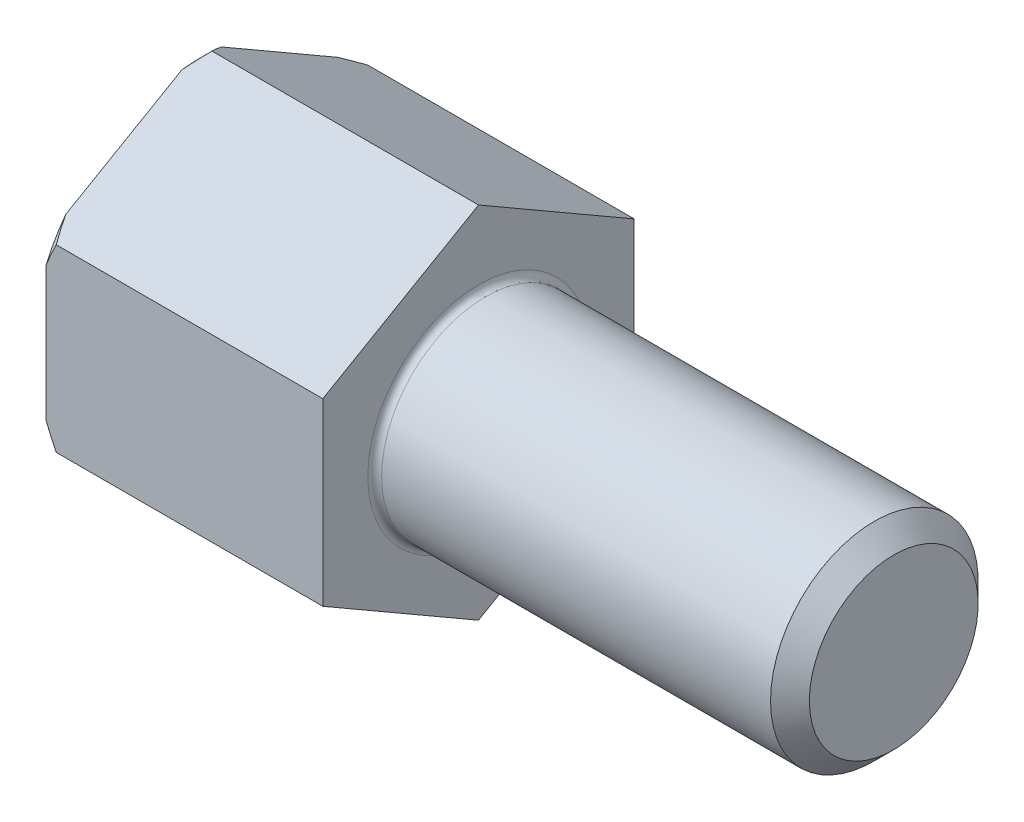
SolidWorks part; units mm, degrees
revolve "Base-Revolve" add sketch "BodySke"
sketch "BodySke" plane through (0, 0, 0) normal (0, 0, 1) x (1, 0, 0)
  line L0 (0, 0) -> (0, 2.45)
  line L1 (0.3, 2.75) -> (4, 2.75)
  line L2 (4, 2.75) -> (4, 1.5)
  line L3 (4, 1.5) -> (9.7195, 1.5)
  line L4 (10, 1.2195) -> (10, 0)
  line L5 (10, 0) -> (0, 0)
  line L6 (-31.75, 0) -> (127, 0) construction
  line L7 (0, 2.45) -> (0.3, 2.75)
  line L8 (10, 1.2195) -> (9.7195, 1.5)
  line L9 (0, -2.45) -> (0.3, -2.75) construction
  line L10 (10, -1.2195) -> (9.7195, -1.5) construction
  line L11 (4.5, 9.525) -> (4.5, 3.175) construction
  line L12 (4, 9.525) -> (4, 3.175) construction
  line L13 (-40, 9.525) -> (-40, 3.175) construction
  dimension "Diameter" = 3
  dimension "Head_ht" = 4
  dimension "Length" = 6
  dimension "Body_ch_ang" = 45
  dimension "Head_dia" = 5.5
  dimension "Head_ch_ang" = 45
  dimension "Minor_dia" = 2.439
  dimension "Advance" = 0.5
  dimension "Thread_nom" = 6
  dimension "Thread_length" = 50
  dimension "Head_ch_ht" = 0.3
cosmetic thread "ThreadCosmetic" [suppressed]
fillet "Fillet1" radius 0.1 1 edges at (4, 0, 1.5)
material "Copper"
ref_plane "Plane1" through (0, 0, 0) normal (0, 0, 1) x (1, 0, 0)
ref_plane "Plane2" through (0, 0, 0) normal (0, 1, 0) x (1, 0, 0)
ref_plane "Plane3" through (0, 0, 0) normal (1, 0, 0) x (0, 0, -1)
sketch "Sketch2" plane through (0, 0, 0) normal (0, 0, 1) x (1, 0, 0)
  line L0 (0, 2.25) -> (2.3, 2.25)
  line L1 (2.3, 2.25) -> (3.599, 0)
  line L2 (-31.75, 0) -> (127, 0) construction
  line L3 (3.599, 0) -> (0, 0)
  line L4 (0, 0) -> (0, 2.25)
  line L5 (0, 2.45) -> (0, -2.45) construction
  line L6 (0, 0) -> (47.625, 0) construction
  line L7 (4, -2.75) -> (4, 2.75) construction
  dimension "D1" = 2.25
  dimension "D2" = 60
revolve "Hex-PreBroach" [suppressed] cut sketch "Sketch2" angle 360 about L6
sketch "Sketch3" plane through (0, 0, 0) normal (-1, 0, 0) x (0, 0.5, 0.866)
  line L0 (1.299, 2.25) -> (-1.299, 2.25)
  line L1 (-1.299, 2.25) -> (-2.5981, 0)
  line L2 (1.299, 2.25) -> (2.5981, 0)
  line L3 (1.299, -2.25) -> (2.5981, 0)
  line L4 (1.299, -2.25) -> (-1.299, -2.25)
  line L5 (-1.299, -2.25) -> (-2.5981, 0)
  dimension "D1" = 2.25
  dimension "D2" = 2.25
  dimension "Hex_size" = 4.5
extrude "Hex" cut sketch "Sketch3" against normal through all flip side to cut
hole_wizard "M3x0.5 Tapped Hole1" positions "Sketch8" profile "Sketch9" tap size "M3x0.5" standard "ANSI Metric"
sketch "Sketch8" plane through (0, 0, 0) normal (1, 0, 0) x (0, 0, -1)
  point P0 (0, 0)
sketch "Sketch9" plane through (0, 0, 0) normal (0, 1, 0) x (0, 0, 1)
  line L0 (0, 0) -> (0, 4.2511)
  line L1 (0, 4.2511) -> (1.25, 3.5)
  line L2 (1.25, 3.5) -> (1.25, 0)
  line L5 (1.25, 0) -> (0, 0)
  line L10 (0, 4.2511) -> (-1.25, 3.5) construction
  line L11 (0, -6.35) -> (0, 107.95) construction
  dimension "Tap Drill Dia." = 2.5
  dimension "Tap Drill Depth" = 3.5
  dimension "Drill Angle" = 118
cosmetic thread "Hole Thread1" parameters "D1"=2.5, "D2"=3
sketch "Sketch4" plane through (0, 0, 0) normal (-1, 0, 0) x (0, 0, 1)
  line L0 (0, 0) -> (1.4605, 0)
  line L1 (0, 0) -> (6.1484, 3.5498) construction
  line L2 (0, 0) -> (0.7302, 1.2648)
  line L3 (1.2009, 0.3267) -> (1.3933, 0.4378)
  line L4 (0.8834, 0.8767) -> (1.0758, 0.9877)
  arc A0 (1.2009, 0.3267) -> (0.8834, 0.8767) centre (0, 0) ccw
  arc A1 (1.4605, 0) -> (1.3933, 0.4378) centre (0, 0) ccw
  arc A2 (0.7302, 1.2648) -> (1.0758, 0.9877) centre (0, 0) cw
  dimension "D1" = 30
  dimension "D2" = 60
  dimension "Spline_p_dim" = 0.635
  dimension "D3" = 0.3175
extrude "Spline" [suppressed] cut sketch "Sketch4" against normal blind 1.3
pattern_circular "CirPattern1" [suppressed] count 6 every 60
sketch "Sketch5" plane through (0, 0, 0) normal (0, 0, 1) x (1, 0, 0)
  line L0 (-31.75, 0) -> (127, 0) construction
  line L2 (0, 2.45) -> (0, -2.45) construction
  circle A0 centre (1.2, 0) radius 0.475
  dimension "Drilled_hole_dia" = 0.95
  dimension "Drilled_hole_loc" = 1.2
extrude "Hole" [suppressed] cut sketch "Sketch5" against normal through all and the other way through all
pattern_circular "Drilled-4" [suppressed] count 2 every 60
pattern_circular "Drilled-6" [suppressed] count 3 every 60
sketch "ThdSchSke" plane through (0, 0, 0) normal (0, 0, 1) x (1, 0, 0)
  line L0 (4.5, -1.2195) -> (4.3036, -1.5)
  line L1 (4.5, -1.2195) -> (4.6964, -1.5)
  line L2 (4.6964, -1.5) -> (4.6964, -1.875)
  line L3 (-3.175, 0) -> (5.1513, 0) construction
  line L5 (4.6964, -1.875) -> (4.3036, -1.875)
  line L6 (4.3036, -1.875) -> (4.3036, -1.5)
  line L7 (0, 2.45) -> (0, -2.45) construction
  dimension "Thread_minor" = 2.439
  dimension "Diameter" = 3
  dimension "Start" = 4.5
revolve "ThreadSchematic" [suppressed] cut sketch "ThdSchSke" angle 360 about L3
pattern_linear "ThdSchPat" [suppressed]
equation "\"D2@Sketch3\" = \"Hex_size@Sketch3\" / 2"
equation "\"D1@Sketch3\" = \"Hex_size@Sketch3\" / 2"
equation "\"D1@Sketch2\" = \"Hex_size@Sketch3\" / 2"
equation "\"D3@Sketch4\" = \"Spline_p_dim@Sketch4\" / 2"
equation "\"Thread_minor@ThreadCosmetic\"  =  \"Minor_dia@BodySke\""
equation "\"D2@CirPattern1\" = 360 / \"Num_teeth@CirPattern1\""
equation "\"Thread_length@ThreadCosmetic\" = ((sgn( (\"Length@BodySke\" - \"Advance@BodySke\" ) - \"Thread_nom@BodySke\" )-1)*( (\"Length@BodySke\" - \"Advance@BodySke\" ) - \"Thread_nom@BodySke\" ))/-2+ \"Thread_nom@BodySke\""
equation "\"Thread_minor@ThdSchSke\" = \"Minor_dia@BodySke\""
equation "\"Diameter@ThdSchSke\" = \"Diameter@BodySke\""
equation "\"Overcut@ThdSchSke\" = \"Diameter@BodySke\" * 1.25"
equation "\"Start@ThdSchSke\" = \"Head_ht@BodySke\" + \"Length@BodySke\" - \"Thread_length@ThreadCosmetic\"  '---Non-countersunk---"
equation "\"Num_threads@ThdSchPat\" = int( \"Thread_length@ThreadCosmetic\" / \"Advance@BodySke\" + 0.999 )  + 1"
equation "\"Advance@ThdSchPat\" = \"Thread_length@ThreadCosmetic\" /  (\"Num_threads@ThdSchPat\" - 1) 'relax it"
equation "\"Num_threads@ThdSchPat\" = \"Num_threads@ThdSchPat\" - sgn( \"Num_threads@ThdSchPat\" - 1) '---chamfered tips only---"
